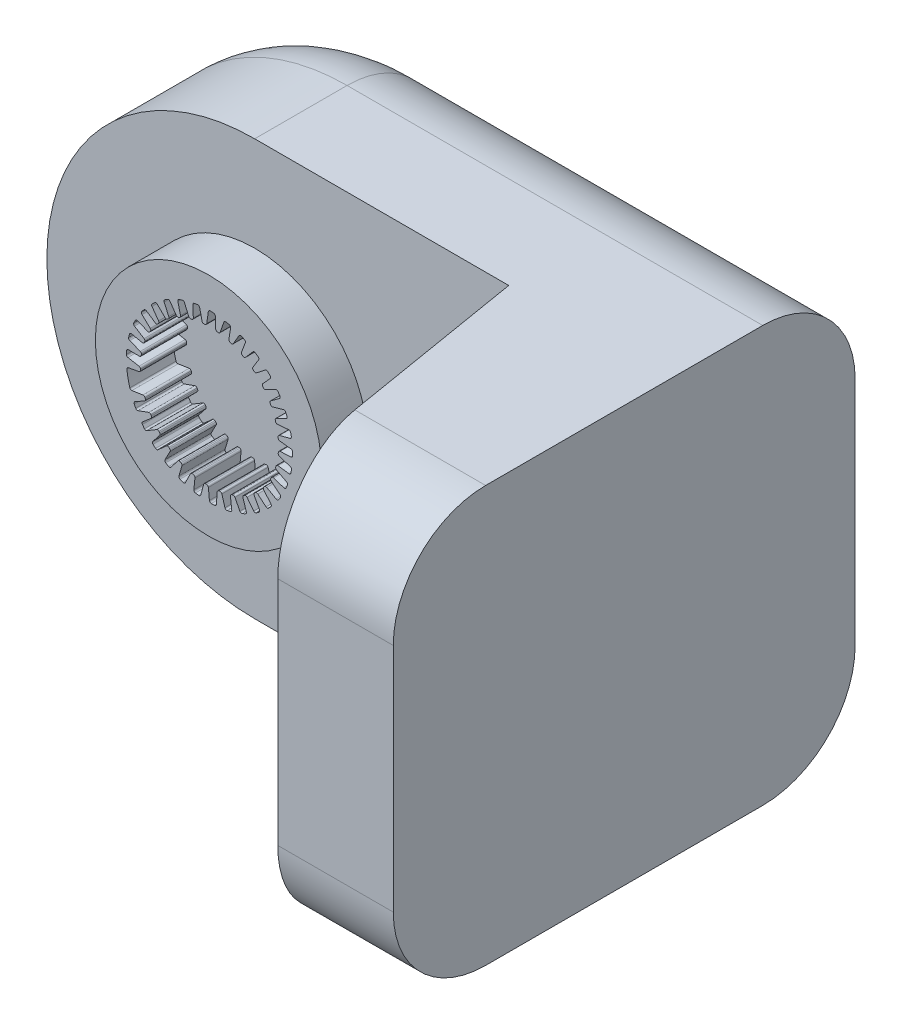
SolidWorks part; units mm, degrees
ref_plane "Front Plane" through (0, 0, 0) normal (0, 0, 1) x (1, 0, 0)
ref_plane "Top Plane" through (0, 0, 0) normal (0, 1, 0) x (1, 0, 0)
ref_plane "Right Plane" through (0, 0, 0) normal (1, 0, 0) x (0, 0, -1)
sketch "Sketch1" plane through (0, 0, 0) normal (0, 0, 1) x (1, 0, 0)
  line L0 (55, 0) -> (-55, 0) construction
  line L1 (-16.9691, -5.4979) -> (-14.565, -5.1246)
  line L2 (-14.1254, -5.3896) -> (-14.0498, -5.609)
  line L3 (-14.2318, -6.0878) -> (-16.2781, -7.2403)
  line L4 (-15.6283, -8.6059) -> (-13.3395, -7.7807)
  line L5 (-12.8575, -7.957) -> (-12.7414, -8.158)
  line L6 (-12.8287, -8.6627) -> (-14.6175, -10.1845)
  line L7 (-13.7191, -11.401) -> (-11.6298, -10.1543)
  line L8 (-11.1229, -10.2354) -> (-10.9707, -10.4105)
  line L9 (-10.96, -10.9225) -> (-12.4256, -12.7577)
  line L10 (-11.3116, -13.7804) -> (-9.4986, -12.158)
  line L11 (-8.9856, -12.1408) -> (-8.8027, -12.2837)
  line L12 (-8.6945, -12.7843) -> (-9.783, -14.8654)
  line L13 (-8.4943, -15.6568) -> (-7.0242, -13.7182)
  line L14 (-6.5239, -13.6035) -> (-6.3171, -13.7088)
  line L15 (-6.1154, -14.1796) -> (-6.7868, -16.4302)
  line L16 (-5.3708, -16.9611) -> (-4.2976, -14.7776)
  line L17 (-3.8283, -14.5696) -> (-3.6053, -14.6335)
  line L18 (-3.3174, -15.0571) -> (-3.5471, -17.3945)
  line L19 (-2.0557, -17.6455) -> (-1.4189, -15.2973)
  line L20 (-0.998, -15.0035) -> (-0.7668, -15.0238)
  line L21 (-0.4034, -15.3847) -> (-0.1828, -17.7229)
  line L22 (1.329, -17.6847) -> (1.5061, -15.2582)
  line L23 (1.8632, -14.8895) -> (2.094, -14.8652)
  line L24 (2.5196, -15.1502) -> (3.1822, -17.4034)
  line L25 (4.659, -17.0774) -> (4.3698, -14.6617)
  line L26 (4.65, -14.2316) -> (4.872, -14.1637)
  line L27 (5.3441, -14.3623) -> (6.4245, -16.4476)
  line L28 (7.8119, -15.8458) -> (7.0671, -13.5297)
  line L29 (7.2601, -13.054) -> (7.465, -12.9451)
  line L30 (7.9664, -13.0499) -> (9.4248, -14.8908)
  line L31 (10.6719, -14.0353) -> (9.4989, -11.9038)
  line L32 (9.5976, -11.4001) -> (9.7779, -11.254)
  line L33 (10.29, -11.2612) -> (12.073, -12.79)
  line L34 (13.1339, -11.7123) -> (11.5757, -9.8438)
  line L35 (11.5765, -9.3305) -> (11.7257, -9.1527)
  line L36 (12.2298, -9.0621) -> (14.2716, -10.2226)
  line L37 (15.1075, -8.9622) -> (13.2214, -7.4254)
  line L38 (13.1242, -6.9214) -> (13.2367, -6.7184)
  line L39 (13.7142, -6.5332) -> (15.94, -7.2828)
  line L40 (16.52, -5.8861) -> (14.3753, -4.7374)
  line L41 (14.1837, -4.2612) -> (14.2555, -4.0405)
  line L42 (14.6889, -3.7676) -> (17.0168, -4.0787)
  line L43 (17.3196, -2.597) -> (14.9951, -1.8786)
  line L44 (14.7162, -1.4477) -> (14.7445, -1.2173)
  line L45 (15.1179, -0.8668) -> (17.4624, -0.728)
  line L46 (17.477, 0.7843) -> (15.0581, 1.0459)
  line L47 (14.7021, 1.4157) -> (14.6859, 1.6472)
  line L48 (14.9856, 2.0626) -> (17.2605, 2.6462)
  line L49 (16.9862, 4.1334) -> (14.5619, 3.9288)
  line L50 (14.1419, 4.2238) -> (14.0818, 4.448)
  line L51 (14.2967, 4.9129) -> (16.4185, 5.9199)
  line L52 (15.8655, 7.3274) -> (13.5247, 6.6639)
  line L53 (13.0561, 6.8734) -> (12.9544, 7.082)
  line L54 (13.0766, 7.5794) -> (14.9673, 8.9727)
  line L55 (14.1559, 10.2489) -> (11.9847, 9.151)
  line L56 (11.4848, 9.2672) -> (11.3451, 9.4525)
  line L57 (11.3702, 9.9641) -> (12.9602, 11.6926)
  line L58 (11.9202, 12.7905) -> (9.9985, 11.2984)
  line L59 (9.4855, 11.3171) -> (9.3131, 11.4724)
  line L60 (9.2401, 11.9793) -> (10.4711, 13.9795)
  line L61 (9.2407, 14.8588) -> (7.6389, 13.0275)
  line L62 (7.1318, 12.9479) -> (6.9329, 13.0675)
  line L63 (6.7645, 13.5511) -> (7.5913, 15.7494)
  line L64 (6.2158, 16.3778) -> (4.9929, 14.2745)
  line L65 (4.5102, 14.0997) -> (4.2922, 14.1791)
  line L66 (4.0346, 14.6217) -> (4.4267, 16.9374)
  line L67 (2.9565, 17.2917) -> (2.1574, 14.9937)
  line L68 (1.7171, 14.73) -> (1.4878, 14.7663)
  line L69 (1.1505, 15.1517) -> (1.0936, 17.4997)
  line L70 (-0.4172, 17.567) -> (-0.7631, 15.1587)
  line L71 (-1.1451, 14.8159) -> (-1.377, 14.8078)
  line L72 (-1.7817, 15.1217) -> (-2.2855, 17.4156)
  line L73 (-3.7814, 17.1934) -> (-3.6615, 14.7634)
  line L74 (-3.971, 14.354) -> (-4.1972, 14.3018)
  line L75 (-4.6543, 14.5327) -> (-5.5866, 16.6884)
  line L76 (-7.0126, 16.1848) -> (-6.4312, 13.8224)
  line L77 (-6.6569, 13.3614) -> (-6.8689, 13.267)
  line L78 (-7.3617, 13.4065) -> (-8.6882, 15.3446)
  line L79 (-9.992, 14.5782) -> (-8.9705, 12.3701)
  line L80 (-9.1041, 11.8745) -> (-9.2942, 11.7414)
  line L81 (-9.8045, 11.7843) -> (-11.4765, 13.4337)
  line L82 (-12.61, 12.4326) -> (-11.1859, 10.46)
  line L83 (-11.2225, 9.948) -> (-11.3837, 9.7811)
  line L84 (-11.8929, 9.7258) -> (-13.8489, 11.0259)
  line L85 (-14.7706, 9.8269) -> (-12.9963, 8.1622)
  line L86 (-12.9345, 7.6527) -> (-13.0609, 7.458)
  line L87 (-13.5501, 7.3066) -> (-15.7182, 8.2096)
  line L88 (-16.3942, 6.8568) -> (-14.3349, 5.5613)
  line L89 (-14.177, 5.0729) -> (-14.264, 4.8577)
  line L90 (-14.7153, 4.6157) -> (-17.0159, 5.0884)
  line L91 (-17.4214, 3.6315) -> (-15.1526, 2.7527)
  line L92 (-14.9045, 2.3034) -> (-14.9488, 2.0756)
  line L93 (-15.3457, 1.7519) -> (-17.6942, 1.777)
  line L94 (-17.8142, 0.2694) -> (-15.4195, -0.1603)
  line L95 (-15.0901, -0.554) -> (-15.0901, -0.7861)
  line L96 (-15.418, -1.1795) -> (-17.7281, -1.6031)
  circle A0 centre (-0.372, 0) radius 24.5
  arc A1 (-18.0536, -2.0399) -> (-17.4139, -5.2165) centre (-0.1596, -0.0893) ccw
  arc A2 (-17.4139, -5.2165) -> (-16.9691, -5.4979) centre (-17.0305, -5.1026) ccw
  arc A3 (-14.1254, -5.3896) -> (-14.565, -5.1246) centre (-14.5036, -5.5198) ccw
  arc A4 (-14.2318, -6.0878) -> (-14.0498, -5.609) centre (-14.4281, -5.7393) ccw
  arc A5 (-16.2781, -7.2403) -> (-16.4437, -7.7593) centre (-16.0818, -7.5889) ccw
  arc A6 (-16.4437, -7.7593) -> (-16.1186, -8.4146) centre (-0.1596, -0.0893) ccw
  arc A7 (-16.1186, -8.4146) -> (-15.6283, -8.6059) centre (-15.764, -8.2296) ccw
  arc A8 (-12.8575, -7.957) -> (-13.3395, -7.7807) centre (-13.2039, -8.157) ccw
  arc A9 (-12.8287, -8.6627) -> (-12.7414, -8.158) centre (-13.0878, -8.358) ccw
  arc A10 (-14.6175, -10.1845) -> (-14.681, -10.7255) centre (-14.3583, -10.4892) ccw
  arc A11 (-14.681, -10.7255) -> (-14.2369, -11.3068) centre (-0.1596, -0.0893) ccw
  arc A12 (-14.2369, -11.3068) -> (-13.7191, -11.401) centre (-13.924, -11.0575) ccw
  arc A13 (-11.1229, -10.2354) -> (-11.6298, -10.1543) centre (-11.4248, -10.4978) ccw
  arc A14 (-10.96, -10.9225) -> (-10.9707, -10.4105) centre (-11.2726, -10.6729) ccw
  arc A15 (-12.4256, -12.7577) -> (-12.3847, -13.3009) centre (-12.1131, -13.0073) ccw
  arc A16 (-12.3847, -13.3009) -> (-11.8378, -13.7868) centre (-0.1596, -0.0893) ccw
  arc A17 (-11.8378, -13.7868) -> (-11.3116, -13.7804) centre (-11.5783, -13.4824) ccw
  arc A18 (-8.9856, -12.1408) -> (-9.4986, -12.158) centre (-9.2318, -12.456) ccw
  arc A19 (-8.6945, -12.7843) -> (-8.8027, -12.2837) centre (-9.049, -12.5989) ccw
  arc A20 (-9.783, -14.8654) -> (-9.6392, -15.3909) centre (-9.4286, -15.0508) ccw
  arc A21 (-9.6392, -15.3909) -> (-9.0097, -15.7634) centre (-0.1596, -0.0893) ccw
  arc A22 (-9.0097, -15.7634) -> (-8.4943, -15.6568) centre (-8.813, -15.4151) ccw
  arc A23 (-6.5239, -13.6035) -> (-7.0242, -13.7182) centre (-6.7055, -13.9599) ccw
  arc A24 (-6.1154, -14.1796) -> (-6.3171, -13.7088) centre (-6.4987, -14.0653) ccw
  arc A25 (-6.7868, -16.4302) -> (-6.5454, -16.9185) centre (-6.4035, -16.5446) ccw
  arc A26 (-6.5454, -16.9185) -> (-5.8563, -17.1641) centre (-0.1596, -0.0893) ccw
  arc A27 (-5.8563, -17.1641) -> (-5.3708, -16.9611) centre (-5.7297, -16.7847) ccw
  arc A28 (-3.8283, -14.5696) -> (-4.2976, -14.7776) centre (-3.9386, -14.9541) ccw
  arc A29 (-3.3174, -15.0571) -> (-3.6053, -14.6335) centre (-3.7155, -15.018) ccw
  arc A30 (-3.5471, -17.3945) -> (-3.2169, -17.8278) centre (-3.149, -17.4336) ccw
  arc A31 (-3.2169, -17.8278) -> (-2.4937, -17.9374) centre (-0.1596, -0.0893) ccw
  arc A32 (-2.4937, -17.9374) -> (-2.0557, -17.6455) centre (-2.4418, -17.5408) ccw
  arc A33 (-0.998, -15.0035) -> (-1.4189, -15.2973) centre (-1.0328, -15.402) ccw
  arc A34 (-0.4034, -15.3847) -> (-0.7668, -15.0238) centre (-0.8016, -15.4222) ccw
  arc A35 (-0.1828, -17.7229) -> (0.2239, -18.0853) centre (0.2154, -17.6853) ccw
  arc A36 (0.2239, -18.0853) -> (0.9548, -18.0548) centre (-0.1596, -0.0893) ccw
  arc A37 (0.9548, -18.0548) -> (1.329, -17.6847) centre (0.93, -17.6556) ccw
  arc A38 (1.8632, -14.8895) -> (1.5061, -15.2582) centre (1.905, -15.2873) ccw
  arc A39 (2.5196, -15.1502) -> (2.094, -14.8652) centre (2.1358, -15.263) ccw
  arc A40 (3.1822, -17.4034) -> (3.6506, -17.6814) centre (3.566, -17.2905) ccw
  arc A41 (3.6506, -17.6814) -> (4.3623, -17.5121) centre (-0.1596, -0.0893) ccw
  arc A42 (4.3623, -17.5121) -> (4.659, -17.0774) centre (4.2618, -17.1249) ccw
  arc A43 (4.65, -14.2316) -> (4.3698, -14.6617) centre (4.767, -14.6141) ccw
  arc A44 (5.3441, -14.3623) -> (4.872, -14.1637) centre (4.9889, -14.5463) ccw
  arc A45 (6.4245, -16.4476) -> (6.9374, -16.6312) centre (6.7797, -16.2636) ccw
  arc A46 (6.9374, -16.6312) -> (7.6036, -16.3292) centre (-0.1596, -0.0893) ccw
  arc A47 (7.6036, -16.3292) -> (7.8119, -15.8458) centre (7.4311, -15.9683) ccw
  arc A48 (7.2601, -13.054) -> (7.0671, -13.5297) centre (7.4479, -13.4072) ccw
  arc A49 (7.9664, -13.0499) -> (7.465, -12.9451) centre (7.6528, -13.2983) ccw
  arc A50 (9.4248, -14.8908) -> (9.9633, -14.9731) centre (9.7384, -14.6424) ccw
  arc A51 (9.9633, -14.9731) -> (10.5597, -14.5495) centre (-0.1596, -0.0893) ccw
  arc A52 (10.5597, -14.5495) -> (10.6719, -14.0353) centre (10.3215, -14.2282) ccw
  arc A53 (9.5976, -11.4001) -> (9.4989, -11.9038) centre (9.8493, -11.7109) ccw
  arc A54 (10.29, -11.2612) -> (9.7779, -11.254) centre (10.0297, -11.5649) ccw
  arc A55 (12.073, -12.79) -> (12.6173, -12.7681) centre (12.3334, -12.4864) ccw
  arc A56 (12.6173, -12.7681) -> (13.1219, -12.2385) centre (-0.1596, -0.0893) ccw
  arc A57 (13.1219, -12.2385) -> (13.1339, -11.7123) centre (12.8267, -11.9685) ccw
  arc A58 (11.5765, -9.3305) -> (11.5757, -9.8438) centre (11.8829, -9.5876) ccw
  arc A59 (12.2298, -9.0621) -> (11.7257, -9.1527) centre (12.0321, -9.4099) ccw
  arc A60 (14.2716, -10.2226) -> (14.8018, -10.0972) centre (14.4693, -9.8748) ccw
  arc A61 (14.8018, -10.0972) -> (15.196, -9.481) centre (-0.1596, -0.0893) ccw
  arc A62 (15.196, -9.481) -> (15.1075, -8.9622) centre (14.8548, -9.2723) ccw
  arc A63 (13.1242, -6.9214) -> (13.2214, -7.4254) centre (13.474, -7.1153) ccw
  arc A64 (13.7142, -6.5332) -> (13.2367, -6.7184) centre (13.5866, -6.9123) ccw
  arc A65 (15.94, -7.2828) -> (16.4365, -7.0586) centre (16.0677, -6.9037) ccw
  arc A66 (16.4365, -7.0586) -> (16.7059, -6.3785) centre (-0.1596, -0.0893) ccw
  arc A67 (16.7059, -6.3785) -> (16.52, -5.8861) centre (16.3311, -6.2387) ccw
  arc A68 (14.1837, -4.2612) -> (14.3753, -4.7374) centre (14.5642, -4.3848) ccw
  arc A69 (14.6889, -3.7676) -> (14.2555, -4.0405) centre (14.6359, -4.1641) ccw
  arc A70 (17.0168, -4.0787) -> (17.4613, -3.7638) centre (17.0698, -3.6822) ccw
  arc A71 (17.4613, -3.7638) -> (17.5961, -3.0448) centre (-0.1596, -0.0893) ccw
  arc A72 (17.5961, -3.0448) -> (17.3196, -2.597) centre (17.2015, -2.9792) ccw
  arc A73 (14.7162, -1.4477) -> (14.9951, -1.8786) centre (15.1133, -1.4964) ccw
  arc A74 (15.1179, -0.8668) -> (14.7445, -1.2173) centre (15.1415, -1.2661) ccw
  arc A75 (17.4624, -0.728) -> (17.8387, -0.3341) centre (17.4388, -0.3287) ccw
  arc A76 (17.8387, -0.3341) -> (17.8338, 0.3974) centre (-0.1596, -0.0893) ccw
  arc A77 (17.8338, 0.3974) -> (17.477, 0.7843) centre (17.434, 0.3866) ccw
  arc A78 (14.7021, 1.4157) -> (15.0581, 1.0459) centre (15.1011, 1.4436) ccw
  arc A79 (14.9856, 2.0626) -> (14.6859, 1.6472) centre (15.085, 1.6751) ccw
  arc A80 (17.2605, 2.6462) -> (17.5547, 3.1046) centre (17.1611, 3.0337) ccw
  arc A81 (17.5547, 3.1046) -> (17.4103, 3.8218) centre (-0.1596, -0.0893) ccw
  arc A82 (17.4103, 3.8218) -> (16.9862, 4.1334) centre (17.0199, 3.7348) ccw
  arc A83 (14.1419, 4.2238) -> (14.5619, 3.9288) centre (14.5283, 4.3274) ccw
  arc A84 (14.2967, 4.9129) -> (14.0818, 4.448) centre (14.4682, 4.5515) ccw
  arc A85 (16.4185, 5.9199) -> (16.6198, 6.426) centre (16.247, 6.2812) ccw
  arc A86 (16.6198, 6.426) -> (16.3413, 7.1024) centre (-0.1596, -0.0893) ccw
  arc A87 (16.3413, 7.1024) -> (15.8655, 7.3274) centre (15.9746, 6.9426) ccw
  arc A88 (13.0561, 6.8734) -> (13.5247, 6.6639) centre (13.4156, 7.0488) ccw
  arc A89 (13.0766, 7.5794) -> (12.9544, 7.082) centre (13.3139, 7.2574) ccw
  arc A90 (14.9673, 8.9727) -> (15.0684, 9.508) centre (14.73, 9.2947) ccw
  arc A91 (15.0684, 9.508) -> (14.6658, 10.1188) centre (-0.1596, -0.0893) ccw
  arc A92 (14.6658, 10.1188) -> (14.1559, 10.2489) centre (14.3364, 9.8919) ccw
  arc A93 (11.4848, 9.2672) -> (11.9847, 9.151) centre (11.8042, 9.5079) ccw
  arc A94 (11.3702, 9.9641) -> (11.3451, 9.4525) centre (11.6646, 9.6932) ccw
  arc A95 (12.9602, 11.6926) -> (12.9573, 12.2373) centre (12.6658, 11.9634) ccw
  arc A96 (12.9573, 12.2373) -> (12.4456, 12.7601) centre (-0.1596, -0.0893) ccw
  arc A97 (12.4456, 12.7601) -> (11.9202, 12.7905) centre (12.1655, 12.4745) ccw
  arc A98 (9.4855, 11.3171) -> (9.9985, 11.2984) centre (9.7532, 11.6144) ccw
  arc A99 (9.2401, 11.9793) -> (9.3131, 11.4724) centre (9.5807, 11.7697) ccw
  arc A100 (10.4711, 13.9795) -> (10.3643, 14.5136) centre (10.1304, 14.1891) ccw
  arc A101 (10.3643, 14.5136) -> (9.7623, 14.9292) centre (-0.1596, -0.0893) ccw
  arc A102 (9.7623, 14.9292) -> (9.2407, 14.8588) centre (9.5418, 14.5954) ccw
  arc A103 (7.1318, 12.9479) -> (7.6389, 13.0275) centre (7.3379, 13.2908) ccw
  arc A104 (6.7645, 13.5511) -> (6.9329, 13.0675) centre (7.1389, 13.4103) ccw
  arc A105 (7.5913, 15.7494) -> (7.3846, 16.2534) centre (7.2169, 15.8902) ccw
  arc A106 (7.3846, 16.2534) -> (6.7143, 16.5464) centre (-0.1596, -0.0893) ccw
  arc A107 (6.7143, 16.5464) -> (6.2158, 16.3778) centre (6.5616, 16.1768) ccw
  arc A108 (4.5102, 14.0997) -> (4.9929, 14.2745) centre (4.6471, 14.4756) ccw
  arc A109 (4.0346, 14.6217) -> (4.2922, 14.1791) centre (4.429, 14.5549) ccw
  arc A110 (4.4267, 16.9374) -> (4.1276, 17.3926) centre (4.0323, 17.0042) ccw
  arc A111 (4.1276, 17.3926) -> (3.4138, 17.5524) centre (-0.1596, -0.0893) ccw
  arc A112 (3.4138, 17.5524) -> (2.9565, 17.2917) centre (3.3343, 17.1604) ccw
  arc A113 (1.7171, 14.73) -> (2.1574, 14.9937) centre (1.7796, 15.1251) ccw
  arc A114 (1.1505, 15.1517) -> (1.4878, 14.7663) centre (1.5504, 15.1614) ccw
  arc A115 (1.0936, 17.4997) -> (0.7131, 17.8895) centre (0.6937, 17.49) ccw
  arc A116 (0.7131, 17.8895) -> (-0.0181, 17.9101) centre (-0.1596, -0.0893) ccw
  arc A117 (-0.0181, 17.9101) -> (-0.4172, 17.567) centre (-0.0212, 17.5101) ccw
  arc A118 (-1.1451, 14.8159) -> (-0.7631, 15.1587) centre (-1.1591, 15.2156) ccw
  arc A119 (-1.7817, 15.1217) -> (-1.377, 14.8078) centre (-1.391, 15.2075) ccw
  arc A120 (-2.2855, 17.4156) -> (-2.7334, 17.7257) centre (-2.6762, 17.3298) ccw
  arc A121 (-2.7334, 17.7257) -> (-3.4552, 17.6064) centre (-0.1596, -0.0893) ccw
  arc A122 (-3.4552, 17.6064) -> (-3.7814, 17.1934) centre (-3.3819, 17.2132) ccw
  arc A123 (-3.971, 14.354) -> (-3.6615, 14.7634) centre (-4.061, 14.7437) ccw
  arc A124 (-4.6543, 14.5327) -> (-4.1972, 14.3018) centre (-4.2871, 14.6915) ccw
  arc A125 (-5.5866, 16.6884) -> (-6.0854, 16.9073) centre (-5.9537, 16.5296) ccw
  arc A126 (-6.0854, 16.9073) -> (-6.7711, 16.6525) centre (-0.1596, -0.0893) ccw
  arc A127 (-6.7711, 16.6525) -> (-7.0126, 16.1848) centre (-6.6242, 16.2804) ccw
  arc A128 (-6.6569, 13.3614) -> (-6.4312, 13.8224) centre (-6.8196, 13.7268) ccw
  arc A129 (-7.3617, 13.4065) -> (-6.8689, 13.267) centre (-7.0316, 13.6324) ccw
  arc A130 (-8.6882, 15.3446) -> (-9.2196, 15.4643) centre (-9.0183, 15.1187) ccw
  arc A131 (-9.2196, 15.4643) -> (-9.8441, 15.0833) centre (-0.1596, -0.0893) ccw
  arc A132 (-9.8441, 15.0833) -> (-9.992, 14.5782) centre (-9.6289, 14.7462) ccw
  arc A133 (-9.1041, 11.8745) -> (-8.9705, 12.3701) centre (-9.3335, 12.2021) ccw
  arc A134 (-9.8045, 11.7843) -> (-9.2942, 11.7414) centre (-9.5236, 12.069) ccw
  arc A135 (-11.4765, 13.4337) -> (-12.021, 13.4498) centre (-11.7574, 13.1489) ccw
  arc A136 (-12.021, 13.4498) -> (-12.5613, 12.9567) centre (-0.1596, -0.0893) ccw
  arc A137 (-12.5613, 12.9567) -> (-12.61, 12.4326) centre (-12.2857, 12.6668) ccw
  arc A138 (-11.2225, 9.948) -> (-11.1859, 10.46) centre (-11.5103, 10.2259) ccw
  arc A139 (-11.8929, 9.7258) -> (-11.3837, 9.7811) centre (-11.6715, 10.0589) ccw
  arc A140 (-13.8489, 11.0259) -> (-14.3864, 10.9378) centre (-14.0703, 10.6928) ccw
  arc A141 (-14.3864, 10.9378) -> (-14.8227, 10.3506) centre (-0.1596, -0.0893) ccw
  arc A142 (-14.8227, 10.3506) -> (-14.7706, 9.8269) centre (-14.4969, 10.1186) ccw
  arc A143 (-12.9345, 7.6527) -> (-12.9963, 8.1622) centre (-13.27, 7.8705) ccw
  arc A144 (-13.5501, 7.3066) -> (-13.0609, 7.458) centre (-13.3963, 7.6759) ccw
  arc A145 (-15.7182, 8.2096) -> (-16.2291, 8.0206) centre (-15.872, 7.8404) ccw
  arc A146 (-16.2291, 8.0206) -> (-16.5454, 7.361) centre (-0.1596, -0.0893) ccw
  arc A147 (-16.5454, 7.361) -> (-16.3942, 6.8568) centre (-16.1812, 7.1954) ccw
  arc A148 (-14.177, 5.0729) -> (-14.3349, 5.5613) centre (-14.5479, 5.2227) ccw
  arc A149 (-14.7153, 4.6157) -> (-14.264, 4.8577) centre (-14.6348, 5.0075) ccw
  arc A150 (-17.0159, 5.0884) -> (-17.4813, 4.8054) centre (-17.0964, 4.6966) ccw
  arc A151 (-17.4813, 4.8054) -> (-17.6659, 4.0975) centre (-0.1596, -0.0893) ccw
  arc A152 (-17.6659, 4.0975) -> (-17.4214, 3.6315) centre (-17.2769, 4.0045) ccw
  arc A153 (-14.9045, 2.3034) -> (-15.1526, 2.7527) centre (-15.2971, 2.3797) ccw
  arc A154 (-15.3457, 1.7519) -> (-14.9488, 2.0756) centre (-15.3414, 2.1519) ccw
  arc A155 (-17.6942, 1.777) -> (-18.097, 1.4103) centre (-17.6984, 1.377) ccw
  arc A156 (-18.097, 1.4103) -> (-18.1432, 0.6803) centre (-0.1596, -0.0893) ccw
  arc A157 (-18.1432, 0.6803) -> (-17.8142, 0.2694) centre (-17.7435, 0.6632) ccw
  arc A158 (-15.0901, -0.554) -> (-15.4195, -0.1603) centre (-15.4901, -0.554) ccw
  arc A159 (-15.418, -1.1795) -> (-15.0901, -0.7861) centre (-15.4901, -0.7861) ccw
  arc A160 (-17.7281, -1.6031) -> (-18.0536, -2.0399) centre (-17.656, -1.9965) ccw
  dimension "D1" = 49
extrude "Boss-Extrude1" add sketch "Sketch1" along normal blind 10
sketch "Sketch6" plane through (0, 0, 0) normal (0, 0, 1) x (1, 0, 0)
  line L0 (-0.372, 0) -> (89.628, 0) construction
  line L1 (-0.372, 45) -> (89.628, 45)
  line L2 (89.628, -45) -> (-0.372, -45)
  line L3 (89.628, 45) -> (89.628, -45)
  arc A2 (-0.372, 45) -> (-0.372, -45) centre (-0.372, 0) ccw
  dimension "D1" = 90
extrude "Boss-Extrude3" add sketch "Sketch6" against normal blind 40
sketch "Sketch7" plane through (0, 0, 0) normal (0, 0, 1) x (1, 0, 0)
  line L0 (-0.372, -45) -> (89.628, -45) construction
  line L1 (89.628, 45) -> (54.628, 45)
  line L2 (89.628, 45) -> (89.628, -45)
  line L3 (89.628, -45) -> (54.628, -45)
  line L4 (54.628, 45) -> (54.628, -45)
  dimension "D1" = 35
extrude "Boss-Extrude4" add sketch "Sketch7" along normal blind 60
sketch "Sketch8" plane through (0, 45, 0) normal (0, 1, 0) x (1, 0, 0)
  line L0 (54.628, 0) -> (64.628, -60)
  line L1 (89.628, -60) -> (54.628, -60) construction
  line L2 (64.628, -60) -> (54.628, -60)
  line L3 (54.628, -60) -> (54.628, 0)
  dimension "D1" = 10
extrude "Cut-Extrude1" cut sketch "Sketch8" against normal through all
fillet "Fillet1" radius 20 3 edges at (44.628, -45, -40) (-45.372, 0, -40) (44.628, 45, -40)
fillet "Fillet2" radius 20 2 edges at (77.128, -45, 60) (77.128, 45, 60)
